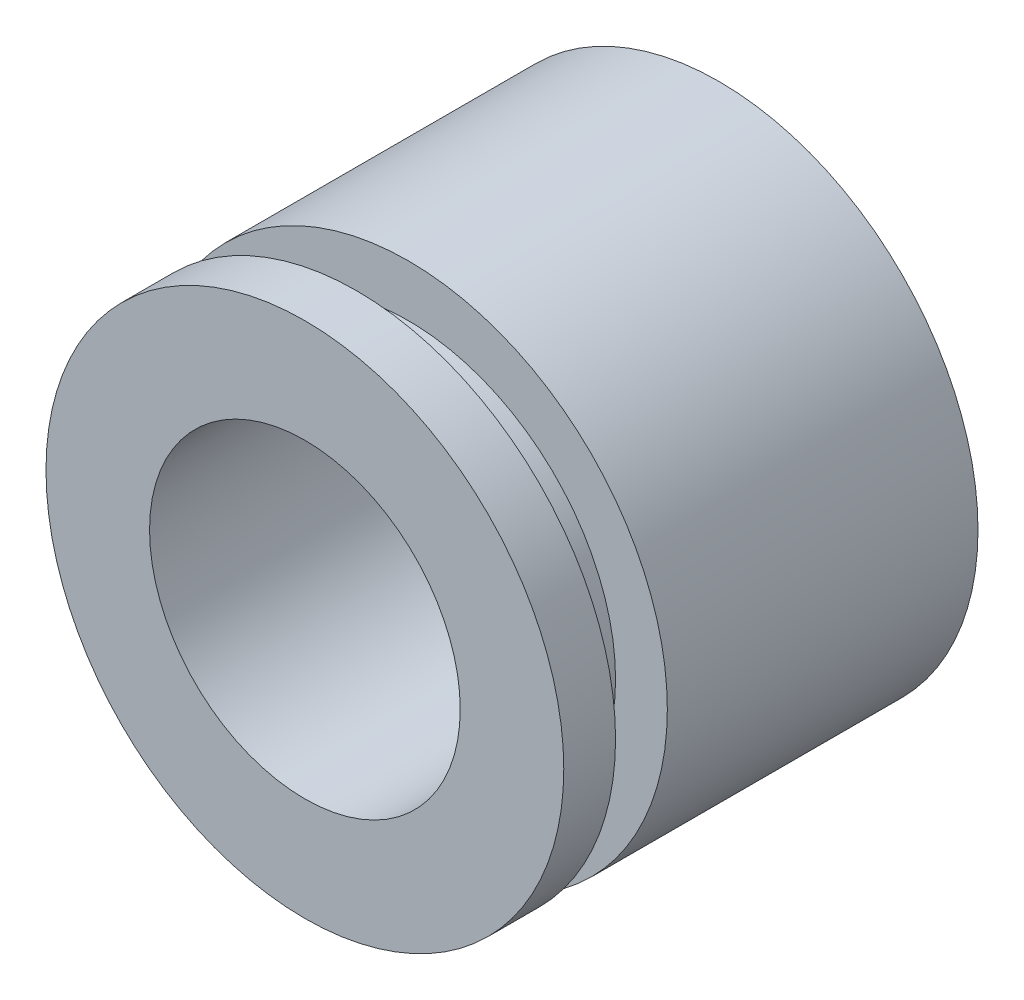
SolidWorks part; units mm, degrees
ref_plane "Front Plane" through (0, 0, 0) normal (0, 0, 1) x (1, 0, 0)
ref_plane "Top Plane" through (0, 0, 0) normal (0, 1, 0) x (1, 0, 0)
ref_plane "Right Plane" through (0, 0, 0) normal (1, 0, 0) x (0, 0, -1)
sketch "Sketch3" plane through (0, 0, 0) normal (0, 0, 1) x (1, 0, 0)
  circle A0 centre (0, 0) radius 63.5
  dimension "D1" = 127
extrude "Boss-Extrude1" add sketch "Sketch3" along normal blind 76.2
sketch "Sketch4" plane through (0, 0, 76.2) normal (0, 0, 1) x (1, 0, 0)
  circle A0 centre (0, 0) radius 50.8
  dimension "D1" = 101.6
extrude "Boss-Extrude2" add sketch "Sketch4" along normal blind 12.7
sketch "Sketch5" plane through (0, 0, 88.9) normal (0, 0, 1) x (1, 0, 0)
  circle A0 centre (0, 0) radius 63.5
  dimension "D1" = 127
extrude "Boss-Extrude3" add sketch "Sketch5" along normal blind 12.7
sketch "Sketch6" plane through (0, 0, 0) normal (0, 0, -1) x (-1, 0, 0)
  circle A0 centre (0, 0) radius 38.1
  dimension "D1" = 76.2
extrude "Cut-Extrude1" cut sketch "Sketch6" against normal through all
sketch "Sketch7" plane through (0, 0, 101.6) normal (0, 0, 1) x (1, 0, 0)
  line L0 (63.5, 0) -> (-63.5, 0)
  arc A0 (-63.5, 0) -> (63.5, 0) centre (0, 0) ccw
